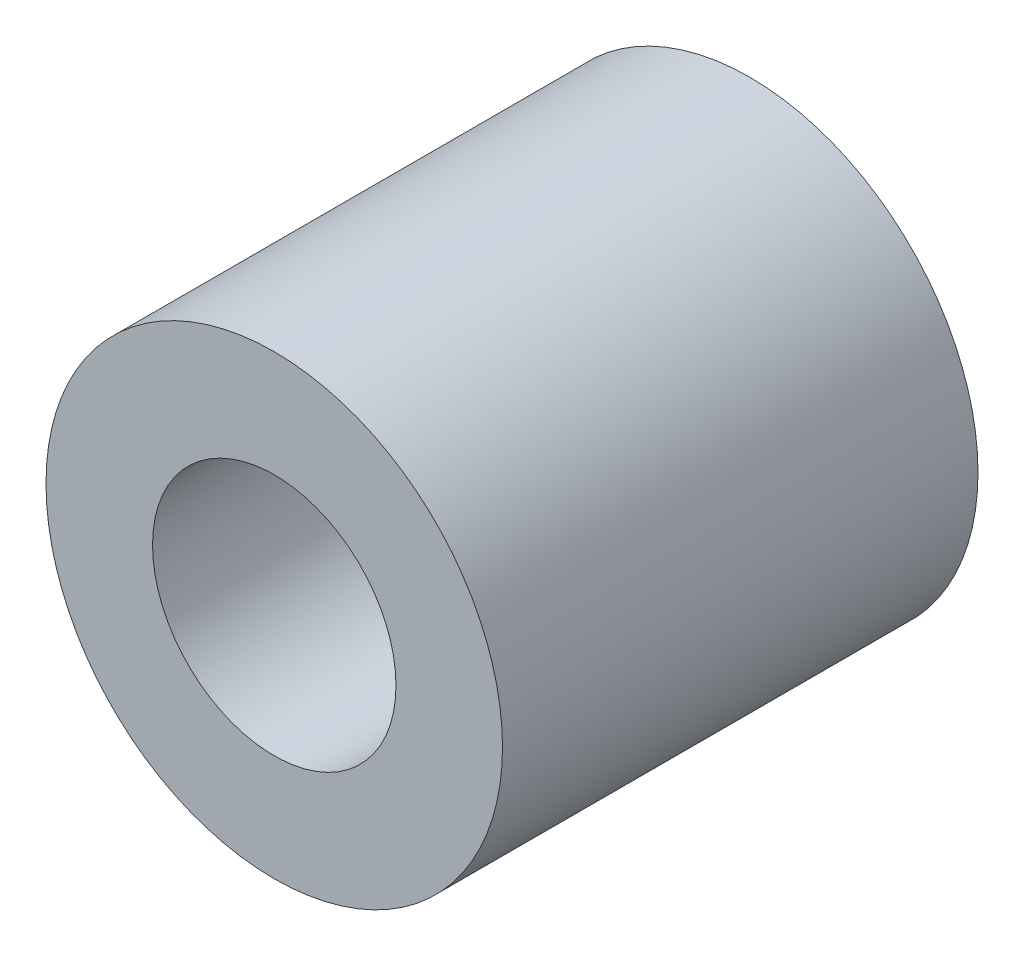
SolidWorks part; units mm, degrees
ref_plane "正面" through (0, 0, 0) normal (0, 0, 1) x (1, 0, 0)
ref_plane "平面" through (0, 0, 0) normal (0, 1, 0) x (1, 0, 0)
ref_plane "右側面" through (0, 0, 0) normal (1, 0, 0) x (0, 0, -1)
sketch "ｽｹｯﾁ1" plane through (0, 0, 0) normal (0, 0, 1) x (1, 0, 0)
  circle A0 centre (0, 0) radius 3
  circle A1 centre (0, 0) radius 1.6
  dimension "D1" = 6
  dimension "D2" = 3.2
extrude "ﾎﾞｽ - 押し出し1" add sketch "ｽｹｯﾁ1" along normal blind 6.25
